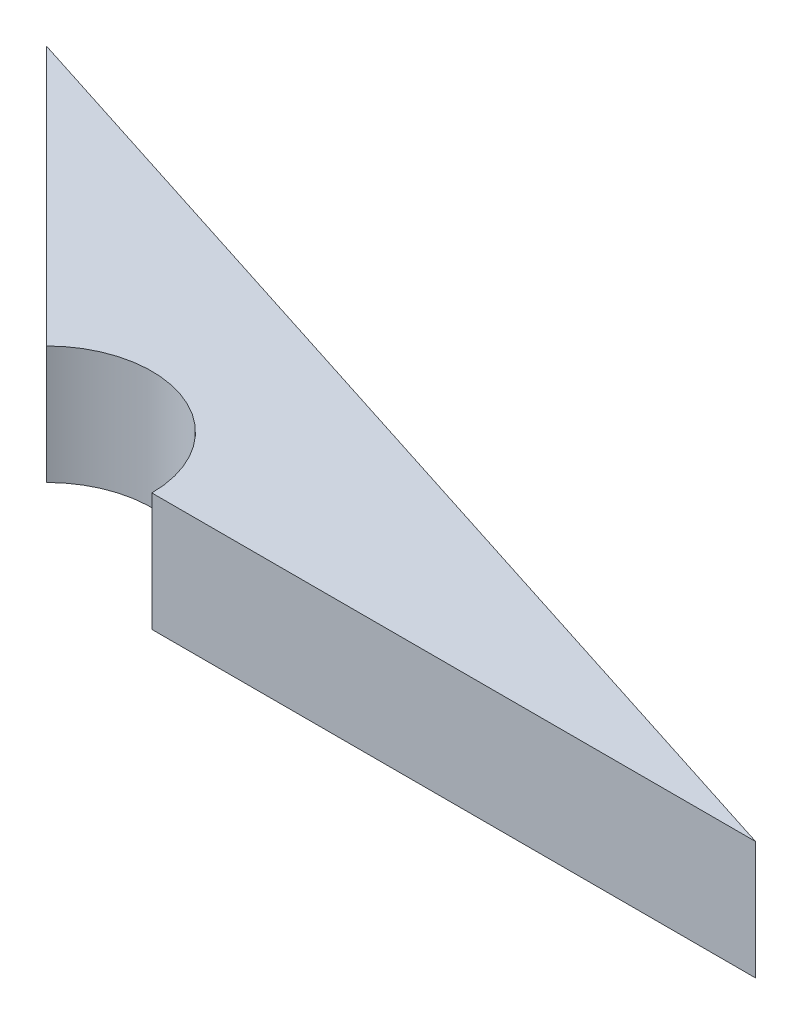
SolidWorks part; units mm, degrees
ref_plane "Front Plane" through (0, 0, 0) normal (0, 0, 1) x (1, 0, 0)
ref_plane "Top Plane" through (0, 0, 0) normal (0, 1, 0) x (1, 0, 0)
ref_plane "Right Plane" through (0, 0, 0) normal (1, 0, 0) x (0, 0, -1)
sketch "Sketch1" plane through (0, 0, 0) normal (0, 1, 0) x (1, 0, 0)
  line L0 (-7.323, -0.368) -> (-32.8627, -0.368)
  line L1 (-51.4651, 13.7741) -> (-40.4769, 2.7859)
  line L2 (-7.323, -0.368) -> (-51.4651, 13.7741)
  arc A0 (-32.8627, -0.368) -> (-40.4769, 2.7859) centre (-37.323, -0.368) ccw
  dimension "D1" = 30
  dimension "D2" = 20
  dimension "D3" = 135
extrude "Boss-Extrude1" add sketch "Sketch1" along normal blind 5
